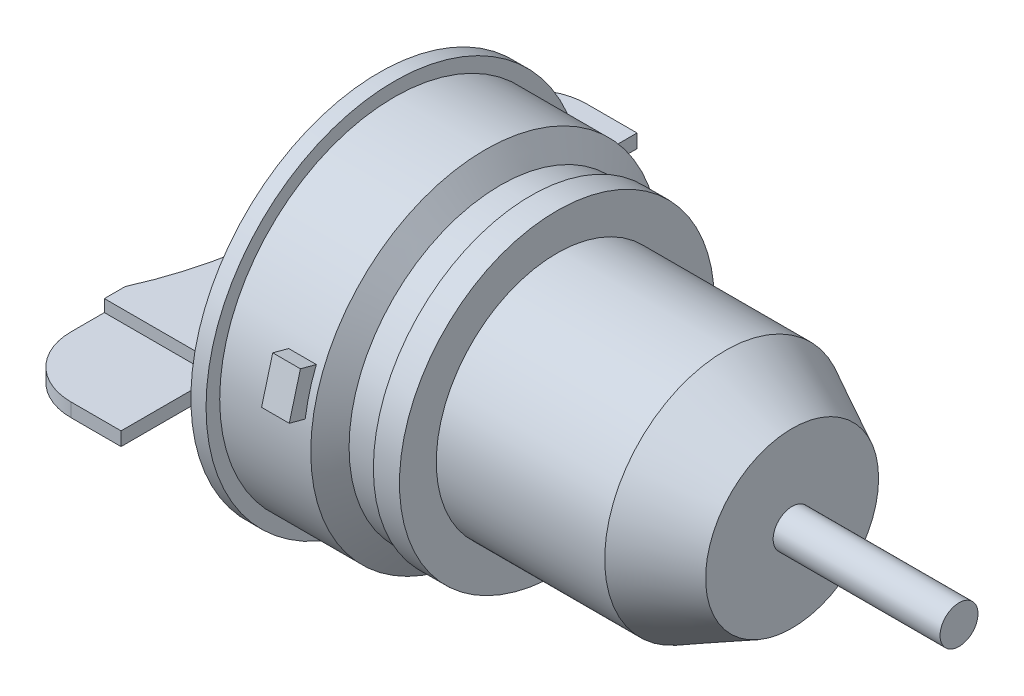
SolidWorks part; units mm, degrees
ref_plane "Front Plane" through (0, 0, 0) normal (0, 0, 1) x (1, 0, 0)
ref_plane "Top Plane" through (0, 0, 0) normal (0, 1, 0) x (1, 0, 0)
ref_plane "Right Plane" through (0, 0, 0) normal (1, 0, 0) x (0, 0, -1)
sketch "Sketch1" plane through (0, 0, 0) normal (1, 0, 0) x (0, 0, -1)
  circle A0 centre (0, 0) radius 20.193
  dimension "D1" = 40.386
extrude "Boss-Extrude1" add sketch "Sketch1" along normal blind 28.194
ref_plane "Plane1" through (28.194, 0, 0) normal (1, 0, 0) x (0, 0, -1)
sketch "Sketch2" plane through (28.194, 0, 0) normal (1, 0, 0) x (0, 0, -1)
  circle A0 centre (0, 0) radius 20.193
  circle A2 centre (0, 0) radius 20.193 construction
ref_plane "Plane2" through (39.37, 0, 0) normal (1, 0, 0) x (0, 0, -1)
sketch "Sketch3" plane through (39.37, 0, 0) normal (1, 0, 0) x (0, 0, -1)
  circle A0 centre (0, 0) radius 14.478
  dimension "D1" = 28.956
loft "Loft2" add profiles "Sketch2", "Sketch3"
sketch "Sketch4" plane through (39.37, 0, 0) normal (1, 0, 0) x (0, 0, -1)
  circle A0 centre (0, 0) radius 3.175
  dimension "D1" = 6.35
extrude "Boss-Extrude2" add sketch "Sketch4" along normal blind 27.94
sketch "Sketch5" plane through (0, 0, 0) normal (1, 0, 0) x (0, 0, -1)
  circle A0 centre (0, 0) radius 26.3525
  dimension "D1" = 52.705
extrude "Boss-Extrude4" add sketch "Sketch5" against normal blind 9.4488 contours A0
sketch "Sketch6" plane through (-9.4488, 0, 0) normal (-1, 0, 0) x (0, 0, 1)
  circle A0 centre (0, 0) radius 25.3365
  circle A1 centre (0, 0) radius 26.3525 construction
  dimension "D1" = 1.016
extrude "Cut-Extrude1" cut sketch "Sketch6" against normal blind 5.08 flip side to cut
ref_plane "Plane3" through (-11.9888, 0, 0) normal (-1, 0, 0) x (0, 0, 1)
sketch "Sketch9" plane through (-11.9888, 0, 0) normal (-1, 0, 0) x (0, 0, 1)
  circle A0 centre (0, 0) radius 29.21
  dimension "D1" = 58.42
loft "Loft3" add profiles "Sketch9" section "Sketch9" section edge at (-9.4488, 0, 25.3365)
sketch "Sketch10" plane through (-11.9888, 0, 0) normal (-1, 0, 0) x (0, 0, 1)
  circle A0 centre (0, 0) radius 29.21
extrude "Boss-Extrude5" add sketch "Sketch10" along normal blind 15.24
sketch "Sketch11" plane through (-27.2288, 0, 0) normal (-1, 0, 0) x (0, 0, 1)
  circle A0 centre (0, 0) radius 31.496
  dimension "D1" = 62.992
extrude "Boss-Extrude6" add sketch "Sketch11" along normal blind 2.54
ref_plane "Plane4" through (-37.3888, 0, 0) normal (-1, 0, 0) x (0, 0, 1)
sketch "Sketch12" plane through (-37.3888, 0, 0) normal (-1, 0, 0) x (0, 0, 1)
  circle A0 centre (0, 0) radius 20.32
  dimension "D1" = 40.64
sketch "Sketch13" plane through (-29.7688, 0, 0) normal (-1, 0, 0) x (0, 0, 1)
  circle A0 centre (0, 0) radius 31.496
  circle A1 centre (0, 0) radius 31.496 construction
sketch "Sketch14" plane through (-29.7688, 0, 0) normal (-1, 0, 0) x (0, 0, 1)
  circle A0 centre (0, 0) radius 22.225
  dimension "D1" = 44.45
loft "Loft6" add profiles "Sketch14", "Sketch12"
sketch "Sketch15" plane through (0, 0, 0) normal (0, 0, 1) x (1, 0, 0)
  line L0 (-29.7688, 31.496) -> (-29.7688, -31.496) construction
  line L1 (-29.7688, 3.175) -> (-48.3108, 3.175)
  line L2 (-29.7688, 3.175) -> (-29.7688, -3.175)
  line L3 (-29.7688, -3.175) -> (-48.3108, -3.175)
  line L4 (-48.3108, 3.175) -> (-48.3108, -3.175)
  line L5 (-29.7688, 3.175) -> (-48.3108, -3.175) construction
  line L6 (-29.7688, -3.175) -> (-48.3108, 3.175) construction
  point P4 (-39.0398, 0)
  dimension "D1" = 6.35
  dimension "D2" = 18.542
extrude "Boss-Extrude7" add sketch "Sketch15" along normal mid plane 86.36
sketch "Sketch16" plane through (0, 0, 43.18) normal (0, 0, 1) x (1, 0, 0)
  line L0 (-48.3108, 3.175) -> (-48.3108, -3.175) construction
  line L1 (-48.3108, 1.143) -> (-29.7688, 1.143)
  line L2 (-48.3108, 1.143) -> (-48.3108, -1.143)
  line L3 (-48.3108, -1.143) -> (-29.7688, -1.143)
  line L4 (-29.7688, 1.143) -> (-29.7688, -1.143)
  line L5 (-48.3108, 1.143) -> (-29.7688, -1.143) construction
  line L6 (-48.3108, -1.143) -> (-29.7688, 1.143) construction
  line L7 (-29.7688, 31.496) -> (-29.7688, -31.496) construction
  line L8 (-48.3108, 0) -> (-29.7688, 0) construction
  line L10 (-48.3108, 1.143) -> (-29.7688, 1.143)
  line L11 (-48.3108, 1.143) -> (-48.3108, 3.175)
  line L12 (-48.3108, 3.175) -> (-29.7688, 3.175)
  line L13 (-29.7688, 1.143) -> (-29.7688, 3.175)
  line L14 (-48.3108, 1.143) -> (-29.7688, 3.175) construction
  line L15 (-48.3108, 3.175) -> (-29.7688, 1.143) construction
  line L16 (-48.3108, -1.143) -> (-29.7688, -1.143)
  line L17 (-48.3108, -1.143) -> (-48.3108, -3.175)
  line L18 (-48.3108, -3.175) -> (-29.7688, -3.175)
  line L19 (-29.7688, -1.143) -> (-29.7688, -3.175)
  line L20 (-48.3108, -1.143) -> (-29.7688, -3.175) construction
  line L21 (-48.3108, -3.175) -> (-29.7688, -1.143) construction
  point P4 (-39.0398, 0)
  point P10 (-48.3108, 0)
  point P15 (-39.0398, 2.159)
  point P18 (-39.0398, -2.159)
  line M5 (-29.7688, -3.175) -> (-29.7688, 3.175)
  line M6 (-29.7688, 3.175) -> (-48.3108, 3.175)
  line M7 (-48.3108, 3.175) -> (-48.3108, -3.175)
  line M8 (-48.3108, -3.175) -> (-29.7688, -3.175)
  dimension "D1" = 2.286
extrude "Cut-Extrude2" cut sketch "Sketch16" against normal blind 15.748 contours L1 M7 M5 M6 | L3 M7 M8 M5
mirror "Mirror1" about plane through (0, 0, 0) normal (0, 0, 1) of "Cut-Extrude2"
sketch "Sketch17" plane through (-37.3888, 0, 0) normal (-1, 0, 0) x (0, 0, 1)
  line L0 (20.0704, -3.175) -> (-20.0704, -3.175) construction
  circle A0 centre (0, -11.811) radius 5.461
  dimension "D1" = 10.922
  dimension "D2" = 8.636
extrude "Boss-Extrude8" add sketch "Sketch17" along normal blind 10.16 draft 1
sketch "Sketch18" plane through (0, 3.175, 0) normal (0, 1, 0) x (1, 0, 0)
  line L0 (-48.3108, -27.432) -> (-48.3108, 27.432) construction
  line L1 (-48.3108, 23.9407) -> (-48.3108, -23.9407)
  arc A0 (-48.3108, 23.9407) -> (-48.3108, -23.9407) centre (-101.6, 0) cw
  dimension "D1" = 58.42
  dimension "D2" = 101.6
extrude "Cut-Extrude3" cut sketch "Sketch18" against normal up to next
fillet "Fillet1" radius 10.16 1 edges at (-48.3108, 0, -43.18)
fillet "Fillet2" [suppressed] radius 2.54
fillet "Fillet3" radius 10.16 1 edges at (-48.3108, 0, 43.18)
fillet "Fillet4" [suppressed] radius 2.54
fillet "Fillet6" [suppressed] radius 1.27
sketch "Sketch19" plane through (0, 0, 0) normal (1, 0, 0) x (0, 0, -1)
  line L0 (0, 0) -> (50.5437, -13.5431) construction
  line L1 (0, 0) -> (61.4452, 0) construction
  dimension "D1" = 15
ref_plane "Plane5" through (0, 0, 0) normal (0, -0.2588, -0.9659) x (-1, 0, 0)
sketch "Sketch20" plane through (0, 0, 0) normal (0, -0.2588, -0.9659) x (-1, 0, 0)
  line L0 (0, 0) -> (51.8275, 0) construction
  line L1 (27.2288, 29.21) -> (27.2288, -29.21) construction
  line L2 (13.1953, 3.6068) -> (17.8308, 3.6068)
  line L3 (13.1953, 3.6068) -> (13.1953, -3.6068)
  line L4 (13.1953, -3.6068) -> (17.8308, -3.6068)
  line L5 (17.8308, 3.6068) -> (17.8308, -3.6068)
  line L6 (13.1953, 3.6068) -> (17.8308, -3.6068) construction
  line L7 (13.1953, -3.6068) -> (17.8308, 3.6068) construction
  point P7 (15.513, 0)
  dimension "D1" = 7.2136
  dimension "D2" = 4.6355
  dimension "D3" = 9.398
extrude "Boss-Extrude9" add sketch "Sketch20" along normal mid plane 63.5
